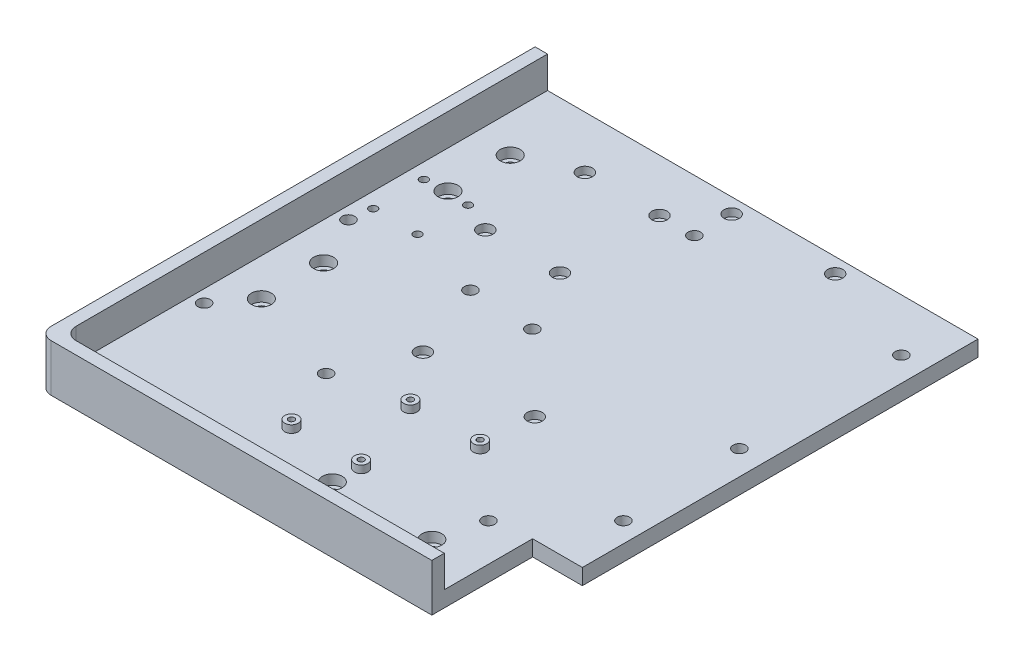
SolidWorks part; units mm, degrees
ref_plane "Front Plane" through (0, 0, 0) normal (0, 0, 1) x (1, 0, 0)
ref_plane "Top Plane" through (0, 0, 0) normal (0, 1, 0) x (1, 0, 0)
ref_plane "Right Plane" through (0, 0, 0) normal (1, 0, 0) x (0, 0, -1)
sketch "Sketch1" plane through (0, 0, 0) normal (0, 1, 0) x (1, 0, 0)
  line L1 (0, 0) -> (158, 0)
  line L2 (0, 0) -> (0, -199.5)
  line L3 (0, -199.5) -> (158, -199.5)
  line L4 (158, 0) -> (158, -199.5)
  dimension "D1" = 158
  dimension "D2" = 199.5
extrude "Boss-Extrude1" add sketch "Sketch1" along normal blind 6.35
sketch "Sketch2" [suppressed] plane through (0, 6.35, 0) normal (0, 1, 0) x (1, 0, 0)
  line L0 (0, -199.5) -> (158, -199.5) construction
  line L1 (81, -199.5) -> (0, -199.5)
  line L2 (81, -199.5) -> (81, -158.5)
  line L3 (81, -158.5) -> (0, -158.5)
  line L4 (0, -199.5) -> (0, -158.5)
  dimension "D1" = 81
  dimension "D2" = 41
sketch "Sketch3" plane through (0, 6.35, 0) normal (0, 1, 0) x (1, 0, 0)
  line L22 (0, 0) -> (0, -199.5) construction
  line L30 (0, -199.5) -> (158, -199.5) construction
  line L34 (0, 0) -> (0, -199.5)
  line L35 (0, -199.5) -> (158, -199.5)
  line L36 (5, 0) -> (5, -194.5)
  line L37 (5, -194.5) -> (158, -194.5)
  line L38 (158, -199.5) -> (158, -194.5)
  line L39 (0, 0) -> (5, 0)
  dimension "D1" = 5
extrude "Boss-Extrude2" add sketch "Sketch3" along normal blind 12.7
sketch "Sketch4" plane through (0, 6.35, 0) normal (0, -1, 0) x (1, 0, 0)
  line L0 (78, 179.5) -> (158, 179.5) construction
  line L3 (0, 199.5) -> (158, 199.5) construction
  line L4 (118, 179.5) -> (118, 188.5903) construction
  line L5 (20, 160) -> (20, 0) construction
  line L7 (158, 0) -> (0, 0) construction
  line L9 (20, 80) -> (152.6176, 80) construction
  line L10 (158, 199.5) -> (158, 0) construction
  line L12 (0, 0) -> (0, 199.5) construction
  point P8 (98, 179.5)
  point P11 (138, 179.5)
  point P20 (20, 130)
  point P21 (20, 105)
  point P22 (20, 30)
  point P23 (20, 80)
  point P24 (20, 55)
  dimension "D1" = 20
  dimension "D2" = 40
  dimension "D3" = 20
  dimension "D4" = 25
  dimension "D5" = 25
  dimension "D6" = 160
  dimension "D7" = 80
hole_wizard "CBORE for M4 SHCS1" positions "Sketch4" profile "Sketch5" counterbore size "M4" standard "ANSI Metric" end condition up to next
sketch "Sketch5" plane through (20, 6.35, 55) normal (1, 0, 0) x (0, 0, 1)
  line L0 (0, 0) -> (0, 6.35)
  line L1 (0, 6.35) -> (2.25, 6.35)
  line L3 (2.25, 6.35) -> (2.25, 4)
  line L4 (2.25, 4) -> (4, 4)
  line L5 (4, 4) -> (4, 0)
  line L7 (4, 0) -> (0, 0)
  line L11 (0, -6.35) -> (0, 107.95) construction
  dimension "Thru Hole Dia." = 4.5
  dimension "Thru Hole Depth" = 6.35
  dimension "C'Bore Dia." = 8
  dimension "C'Bore Depth" = 4
sketch "Sketch7" [suppressed] plane through (0, 0, 0) normal (0, 0, -1) x (-1, 0, 0)
  line L0 (-79, 19.05) -> (-79, 4.7647) construction
  line L2 (-158, 19.05) -> (0, 19.05) construction
  line L3 (-158, 19.05) -> (-29, 19.05)
  line L4 (-158, 19.05) -> (-158, 9.05)
  line L5 (-158, 9.05) -> (-29, 9.05)
  line L6 (-29, 19.05) -> (-29, 9.05)
  line L7 (0, 19.05) -> (0, 0) construction
  line L8 (-158, 6.35) -> (-158, 0) construction
  dimension "D1" = 29
  dimension "D2" = 10
extrude "Cut-Extrude2" [suppressed] cut sketch "Sketch7" against normal up to next
fillet "Fillet1" [suppressed] radius 5
fillet "Fillet2" radius 5 2 edges at (5, 12.7, 194.5) (0, 9.525, 199.5)
sketch "Sketch8" [suppressed] plane through (0, 6.35, 0) normal (0, 1, 0) x (1, 0, 0)
  line L1 (121.3, -179.5) -> (45.1, -179.5) construction
  line L2 (121.3, -179.5) -> (121.3, -52.5) construction
  line L3 (121.3, -52.5) -> (45.1, -52.5) construction
  line L4 (45.1, -179.5) -> (45.1, -52.5) construction
  line L5 (121.3, -179.5) -> (45.1, -52.5) construction
  line L6 (121.3, -52.5) -> (45.1, -179.5) construction
  line L7 (5, -189.5) -> (5, 0) construction
  line L8 (158, -194.5) -> (10, -194.5) construction
  circle A0 centre (45.1, -52.5) radius 3
  circle A1 centre (121.3, -52.5) radius 3
  circle A2 centre (121.3, -179.5) radius 3
  circle A3 centre (45.1, -179.5) radius 3
  point P0 (83.2, -116)
  dimension "D1" = 6
  dimension "D2" = 76.2
  dimension "D3" = 127
  dimension "D4" = 40.1
  dimension "D5" = 15
extrude "Enclosure Mount" [suppressed] cut sketch "Sketch8" against normal through all
sketch "Sketch9" [suppressed] plane through (0, 6.35, 0) normal (0, 1, 0) x (1, 0, 0)
  line L0 (11.75, -15) -> (151.25, -15) construction
  line L2 (158, 0) -> (5, 0) construction
  circle A0 centre (11.75, -15) radius 2.5
  circle A1 centre (151.25, -15) radius 2.5
  point P4 (81.5, 0)
  point P5 (81.5, -15)
  dimension "D1" = 5
  dimension "D2" = 139.5
  dimension "D4" = 15
extrude "Fuse Mount" [suppressed] cut sketch "Sketch9" against normal through all
sketch "Sketch10" [suppressed] plane through (0, 6.35, 0) normal (0, 1, 0) x (1, 0, 0)
  line L0 (158, 0) -> (5, 0) construction
  circle A0 centre (151.25, -34.9) radius 3.05
  circle A1 centre (73.375, -34.9) radius 3.05
  point P4 (151.25, -15)
  dimension "D2" = 6.1
  dimension "D1" = 34.9
  dimension "D3" = 77.875
extrude "Magnets" [suppressed] cut sketch "Sketch10" against normal blind 3.1
sketch "Sketch11" plane through (0, 6.35, 0) normal (0, 1, 0) x (1, 0, 0)
  line L0 (5, -199.5) -> (158, -199.5) construction
  line L1 (158, 0) -> (178, 0)
  line L2 (158, 0) -> (158, -159)
  line L3 (158, -159) -> (178, -159)
  line L4 (178, 0) -> (178, -159)
  dimension "D1" = 40.5
  dimension "D2" = 20
extrude "Boss-Extrude3" add sketch "Sketch11" against normal up to surface (6.35 mm away) up to face at (98, 0, 181.75)
sketch "Sketch12" plane through (0, 6.35, 0) normal (0, 1, 0) x (1, 0, 0)
  line L0 (5, -189.5) -> (5, 0) construction
  line L1 (168.2, -21) -> (85, -21) construction
  line L2 (168.2, -21) -> (168.2, -86.1) construction
  line L3 (168.2, -86.1) -> (85, -86.1) construction
  line L4 (85, -21) -> (85, -86.1) construction
  line L5 (168.2, -21) -> (85, -86.1) construction
  line L6 (168.2, -86.1) -> (85, -21) construction
  line L7 (178, 0) -> (5, 0) construction
  circle A0 centre (168.2, -21) radius 2.5
  circle A1 centre (168.2, -86.1) radius 2.5
  circle A2 centre (85, -86.1) radius 2.5
  circle A3 centre (85, -21) radius 2.5
  point P0 (126.6, -53.55)
  point P10 (168.2, -21)
  point P11 (168.2, -86.1)
  point P12 (85, -86.1)
  point P13 (85, -21)
  dimension "D5" = 5
  dimension "D1" = 65.1
  dimension "D2" = 83.2
  dimension "D3" = 80
  dimension "D4" = 21
extrude "Nucleo" cut sketch "Sketch12" against normal through all
sketch "Sketch13" plane through (0, 6.35, 0) normal (0, 1, 0) x (1, 0, 0)
  line L0 (178, 0) -> (5, 0) construction
  line L1 (59, -85) -> (10, -85) construction
  line L2 (59, -85) -> (59, -143) construction
  line L3 (59, -143) -> (10, -143) construction
  line L4 (10, -85) -> (10, -143) construction
  line L5 (59, -85) -> (10, -143) construction
  line L6 (59, -143) -> (10, -85) construction
  line L7 (5, -189.5) -> (5, 0) construction
  circle A0 centre (59, -143) radius 2.5
  circle A1 centre (10, -143) radius 2.5
  circle A2 centre (10, -85) radius 2.5
  circle A3 centre (59, -85) radius 2.5
  point P0 (34.5, -114)
  dimension "D3" = 5
  dimension "D4" = 85
  dimension "D1" = 58
  dimension "D2" = 49
  dimension "D5" = 5
extrude "PIHolder" cut sketch "Sketch13" against normal through all
sketch "Sketch14" plane through (0, 6.35, 0) normal (0, 1, 0) x (1, 0, 0)
  line L0 (170, -134.5) -> (142.875, -134.5) construction
  line L3 (142.875, -134.5) -> (142.875, -161.625) construction
  line L4 (178, -159) -> (178, 0) construction
  line L5 (158, -159) -> (178, -159) construction
  circle A0 centre (170, -134.5) radius 2.5
  circle A2 centre (142.875, -161.625) radius 2.5
  dimension "D1" = 27.125
  dimension "D2" = 5
  dimension "D3" = 5
  dimension "D4" = 8
  dimension "D5" = 24.5
extrude "ESTOP" cut sketch "Sketch14" against normal through all
sketch "Sketch15" plane through (0, 6.35, 0) normal (0, 1, 0) x (1, 0, 0)
  line L0 (158, -194.5) -> (158, -159) construction
  line L1 (99, -138.1) -> (116, -138.1) construction
  line L2 (99, -138.1) -> (99, -168.9) construction
  line L3 (99, -168.9) -> (116, -168.9) construction
  line L4 (116, -138.1) -> (116, -168.9) construction
  line L5 (99, -138.1) -> (116, -168.9) construction
  line L6 (99, -168.9) -> (116, -138.1) construction
  line L7 (158, -194.5) -> (10, -194.5) construction
  circle A0 centre (116, -138.1) radius 1.2
  circle A1 centre (116, -138.1) radius 2.7
  circle A2 centre (99, -168.9) radius 2.7
  circle A3 centre (99, -168.9) radius 1.2
  point P0 (107.5, -153.5)
  dimension "D3" = 2.4
  dimension "D4" = 1.5
  dimension "D1" = 30.8
  dimension "D2" = 17
  dimension "D5" = 42
  dimension "D6" = 41
extrude "BuckExtrude" add sketch "Sketch15" along normal blind 3
sketch "Sketch16" plane through (0, 6.35, 0) normal (0, 1, 0) x (1, 0, 0)
  circle A0 centre (99, -168.9) radius 1.6
  circle A1 centre (116, -138.1) radius 1.6
  dimension "D1" = 3.2
extrude "BuckCut" cut sketch "Sketch16" against normal through all
pattern_linear "LPattern1" count 2 spacing 28 along (-1, 0, 0) of "BuckExtrude", "BuckCut"
sketch "Sketch17" plane through (0, 6.35, 0) normal (0, 1, 0) x (1, 0, 0)
  line L0 (5, -189.5) -> (5, 0) construction
  line L1 (28.89, -55.84) -> (11.11, -55.84) construction
  line L2 (28.89, -55.84) -> (28.89, -76.16) construction
  line L3 (28.89, -76.16) -> (11.11, -76.16) construction
  line L4 (11.11, -55.84) -> (11.11, -76.16) construction
  line L5 (28.89, -55.84) -> (11.11, -76.16) construction
  line L6 (28.89, -76.16) -> (11.11, -55.84) construction
  line L7 (178, 0) -> (5, 0) construction
  circle A0 centre (28.89, -55.84) radius 1.6
  circle A1 centre (28.89, -76.16) radius 1.6
  circle A2 centre (11.11, -76.16) radius 1.6
  circle A3 centre (11.11, -55.84) radius 1.6
  point P0 (20, -66)
  dimension "D3" = 3.2
  dimension "D1" = 20.32
  dimension "D2" = 17.78
  dimension "D4" = 15
  dimension "D5" = 66
extrude "IMU" cut sketch "Sketch17" against normal through all
sketch "Sketch19" plane through (0, 6.35, 0) normal (0, 1, 0) x (1, 0, 0)
  line L0 (168.2, -21) -> (85, -21) construction
  line L1 (178, 0) -> (5, 0) construction
  line L2 (71, -21) -> (71, -116.1) construction
  line L3 (71, -116.1) -> (116, -116.1) construction
  line L4 (116, -138.1) -> (116, -126.33) construction
  line L5 (59, -85) -> (10, -85) construction
  circle A0 centre (126.6, -6) radius 3.05
  circle A1 centre (85, -6) radius 3.05
  circle A2 centre (116, -116.1) radius 3.05
  circle A3 centre (71, -116.1) radius 3.05
  circle A4 centre (71, -21) radius 3.05
  circle A5 centre (85, -86.1) radius 2.5 construction
  circle A6 centre (71, -61) radius 3.05
  circle A7 centre (41, -61) radius 3.05
  circle A8 centre (41, -21) radius 3.05
  point P6 (126.6, -21)
  point P20 (116, -116.1)
  dimension "D1" = 6.1
  dimension "D3" = 30
  dimension "D2" = 6
  dimension "D4" = 14
  dimension "D5" = 40
  dimension "D6" = 30
extrude "Cut-Extrude8" cut sketch "Sketch19" against normal blind 3.1
sketch "Sketch20" plane through (0, 6.35, 0) normal (0, 1, 0) x (1, 0, 0)
  line L0 (28.89, -55.84) -> (28.89, -76.16) construction
  line L1 (28.89, -76.16) -> (11.11, -76.16) construction
  line L2 (11.11, -76.16) -> (28.89, -55.84) construction
  point P4 (20, -66)
equation "\"D4@Sketch8\"=38.1+2"
equation "\"D5@Sketch8\"=12.7+2.3"
